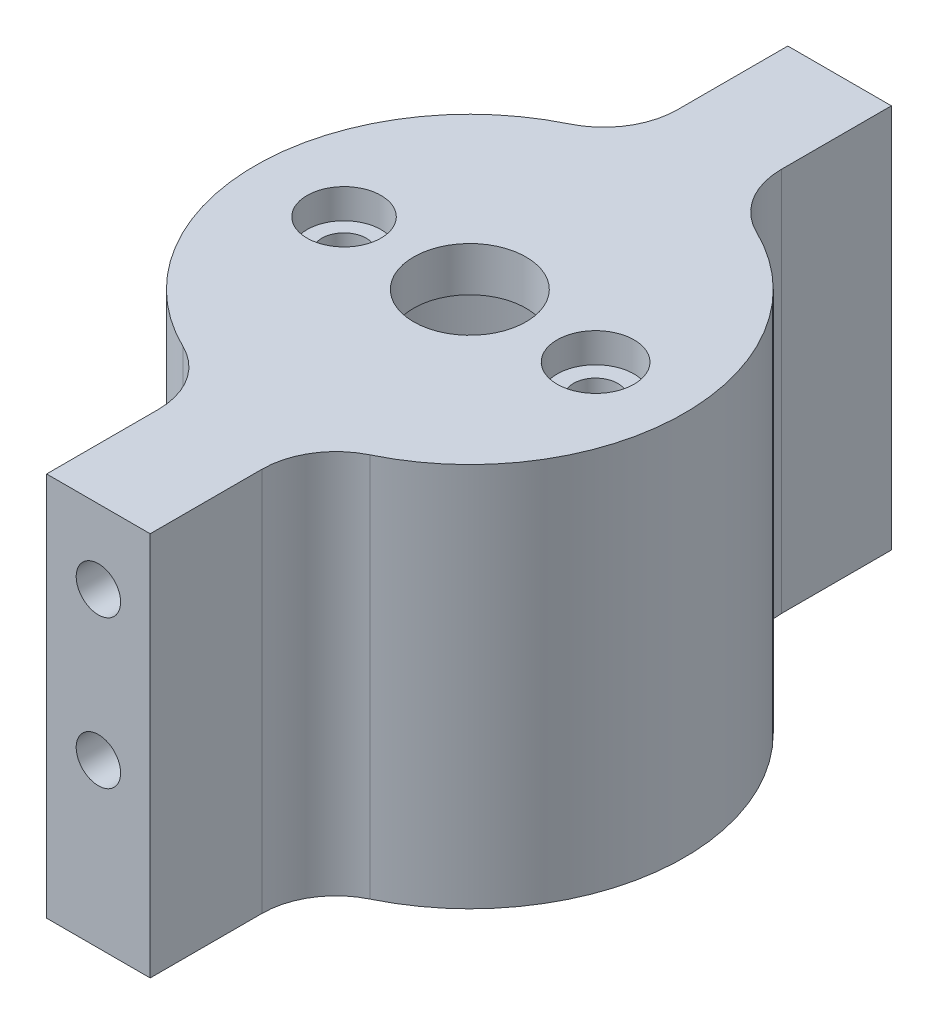
SolidWorks part; units mm, degrees
other "Markup1"
sketch "Sketch11" plane through (-17.3474, -40, -17.5082) normal (-0.1763, -0.9804, -0.0883) x (-0.1909, 0.1221, -0.974)
ref_plane "Front Plane" through (0, 0, 0) normal (0, 0, 1) x (1, 0, 0)
ref_plane "Top Plane" through (0, 0, 0) normal (0, 1, 0) x (1, 0, 0)
ref_plane "Right Plane" through (0, 0, 0) normal (1, 0, 0) x (0, 0, -1)
sketch "Sketch1" plane through (0, 0, 0) normal (0, 1, 0) x (1, 0, 0)
  circle A0 centre (0, 0) radius 14.5
extrude "Boss-Extrude1" add sketch "Sketch1" along normal blind 2 contours A0
sketch "Sketch2" plane through (0, 2, 0) normal (0, 1, 0) x (1, 0, 0)
  line L0 (0, 0) -> (-8.5, 0) construction
  line L1 (0, 0) -> (0, -2.0986) construction
  circle A0 centre (0, 0) radius 3.8
  circle A1 centre (-8.5, 0) radius 1.5
  circle A2 centre (8.5, 0) radius 1.5
  dimension "D1" = 8.5
extrude "Cut-Extrude1" cut sketch "Sketch2" against normal blind 2.5
sketch "Sketch3" plane through (0, 0, 0) normal (0, -1, 0) x (1, 0, 0)
  circle A0 centre (0, 0) radius 14.5
  circle A1 centre (0, 0) radius 12.5
  circle M3 centre (8.5, 0) radius 1.5
  circle M4 centre (-8.5, 0) radius 1.5
  circle M5 centre (0, 0) radius 3.8
  dimension "D1" = 2
extrude "Boss-Extrude2" add sketch "Sketch3" along normal blind 23 contours A1 M3 M5 M4 | A0
sketch "Sketch4" plane through (0, 2, 0) normal (0, 1, 0) x (1, 0, 0)
  circle A0 centre (0, 0) radius 3.8
  circle A1 centre (8.5, 0) radius 1.5
  circle A2 centre (-8.5, 0) radius 1.5
  circle A3 centre (0, 0) radius 14.5
extrude "Boss-Extrude3" add sketch "Sketch4" along normal blind 1 contours A3 | A2 | A1 | A0
sketch "Sketch5" plane through (0, 3, 0) normal (0, 1, 0) x (1, 0, 0)
  line L0 (0, 0) -> (0, 9.3425) construction
  circle A0 centre (8.5, 0) radius 2.6
  circle A1 centre (-8.5, 0) radius 2.5
extrude "Cut-Extrude2" cut sketch "Sketch5" against normal blind 2
sketch "Sketch12" plane through (0, -23, 0) normal (0, -1, 0) x (1, 0, 0)
  line L0 (0, -14.5) -> (0, -25.1) construction
  line L1 (3.5, -25.1) -> (-3.5, -25.1)
  line L2 (-3.5, -25.1) -> (-3.5, -14.0712)
  line L3 (3.5, -25.1) -> (3.5, -14.0712)
  circle A0 centre (0, 0) radius 14.5 construction
  arc A1 (-3.5, -14.0712) -> (3.5, -14.0712) centre (0, 0) ccw
  dimension "D1" = 10.6
  dimension "D2" = 3.5
extrude "Boss-Extrude4" add sketch "Sketch12" against normal blind 26
sketch "Sketch14" plane through (0, 0, -25.1) normal (0, 0, -1) x (-1, 0, 0)
  line L0 (-14.5, -23) -> (14.5, -23) construction
  line L1 (-3.5, 3) -> (3.5, 3)
  line L2 (-3.5, 3) -> (-3.5, -23)
  line L3 (-3.5, -23) -> (3.5, -23)
  line L4 (3.5, 3) -> (3.5, -23)
  line L5 (3.5, 3) -> (3.5, -23) construction
extrude "Cut-Extrude3" cut sketch "Sketch14" against normal blind 0.11 contours L2 L1 L4 L3
sketch "Sketch16" plane through (0, 0, -24.99) normal (0, 0, -1) x (-1, 0, 0)
  line L0 (0, 3) -> (0, -2) construction
  line L1 (-3.5, 3) -> (3.5, 3) construction
  line L2 (0, -2) -> (0, -12) construction
  circle A0 centre (0, -2) radius 1.5
  circle A1 centre (0, -12) radius 1.5
  dimension "D1" = 5
  dimension "D2" = 10
extrude "Cut-Extrude4" cut sketch "Sketch16" against normal blind 6
sketch "Sketch17" plane through (0, 3, 0) normal (0, 1, 0) x (1, 0, 0)
  line L0 (0, 0) -> (0, 24.99) construction
  line L1 (3.5, 24.99) -> (-3.5, 24.99) construction
sketch "Sketch18" plane through (0, -23, 0) normal (0, -1, 0) x (1, 0, 0)
  line L0 (0, 14.5) -> (0, 25.1) construction
  line L1 (3.5, 25.1) -> (-3.5, 25.1)
  line L2 (-3.5, 25.1) -> (-3.5, 14.0712)
  line L3 (3.5, 25.1) -> (3.5, 14.0712)
  arc A0 (3.5, -14.0712) -> (-3.5, -14.0712) centre (0, 0) ccw construction
  arc A1 (3.5, 14.0712) -> (-3.5, 14.0712) centre (0, 0) ccw
  dimension "D1" = 10.6
  dimension "D2" = 3.5
extrude "Boss-Extrude5" add sketch "Sketch18" against normal through all contours A1 L2 L1 L3
sketch "Sketch19" plane through (0, 0, 25.1) normal (0, 0, 1) x (1, 0, 0)
  line L0 (-3.5, 3) -> (3.5, 3) construction
  line L1 (0, 3) -> (0, -2) construction
  line L2 (0, -2) -> (0, -12) construction
  circle A0 centre (0, -2) radius 1.5
  circle A1 centre (0, -12) radius 1.5
  dimension "D1" = 5
  dimension "D2" = 10
extrude "Cut-Extrude5" cut sketch "Sketch19" against normal blind 5
fillet "Fillet1" radius 5 4 edges at (-3.5, -10, -14.0712) (3.5, -10, -14.0712) (3.5, -10, 14.0712) (-3.5, -10, 14.0712)
